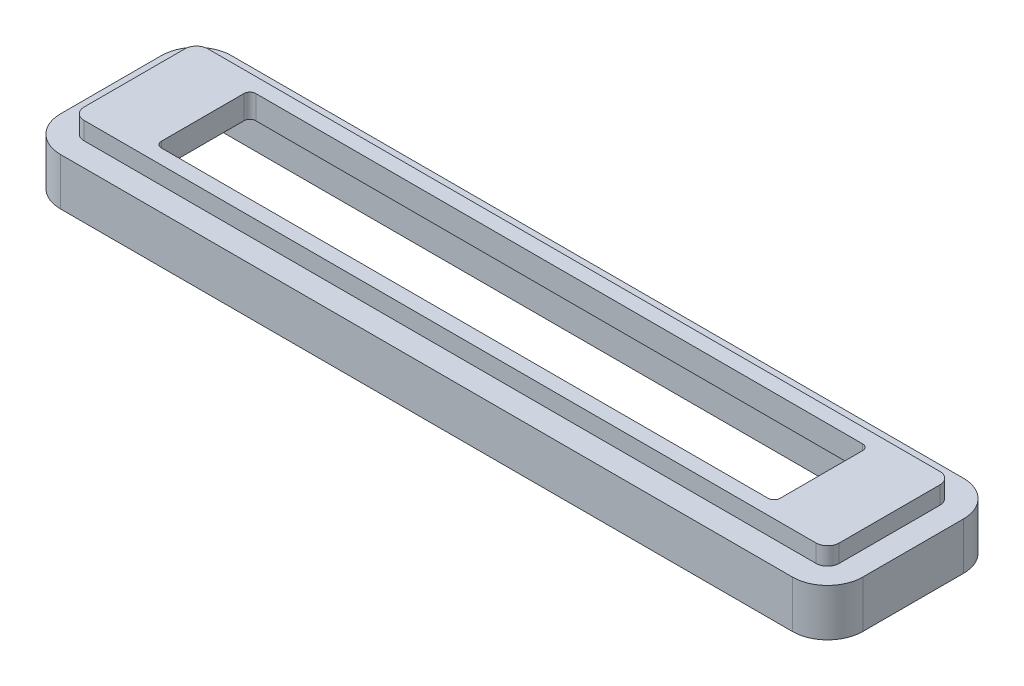
SolidWorks part; units mm, degrees
material "NEOPRENE"
ref_plane "Front Plane" through (0, 0, 0) normal (0, 0, 1) x (1, 0, 0)
ref_plane "Top Plane" through (0, 0, 0) normal (0, 1, 0) x (1, 0, 0)
ref_plane "Right Plane" through (0, 0, 0) normal (1, 0, 0) x (0, 0, -1)
sketch "Sketch1" plane through (0, 0, 0) normal (0, 1, 0) x (1, 0, 0)
  line L0 (-26.215, 3.5) -> (-26.215, -3.5)
  line L1 (-31.0185, -5.25) -> (31.0185, -5.25)
  line L2 (-32, -4.2685) -> (-32, 4.2685)
  line L3 (-31.0185, 5.25) -> (31.0185, 5.25)
  line L4 (32, -4.2685) -> (32, 4.2685)
  line L5 (-32, -5.25) -> (32, 5.25) construction
  line L6 (-32, 5.25) -> (32, -5.25) construction
  line L7 (-25.865, 3.65) -> (25.865, 3.65) construction
  line L8 (-25.865, 3.65) -> (-25.865, -3.65) construction
  line L9 (-25.865, -3.65) -> (25.865, -3.65) construction
  line L10 (25.865, 3.65) -> (25.865, -3.65) construction
  line L11 (-25.865, 3.65) -> (25.865, -3.65) construction
  line L12 (-25.865, -3.65) -> (25.865, 3.65) construction
  line L13 (-25.715, -4) -> (25.715, -4)
  line L14 (26.215, 3.5) -> (26.215, -3.5)
  line L15 (-25.715, 4) -> (25.715, 4)
  line L16 (-26.215, -4) -> (26.215, -4) construction
  line L17 (26.215, 4) -> (26.215, -4) construction
  line L18 (-26.215, 4) -> (26.215, 4) construction
  line L19 (-26.215, 4) -> (-26.215, -4) construction
  arc A0 (31.0185, -5.25) -> (32, -4.2685) centre (31.0185, -4.2685) ccw
  arc A1 (32, 4.2685) -> (31.0185, 5.25) centre (31.0185, 4.2685) ccw
  arc A2 (-31.0185, -5.25) -> (-32, -4.2685) centre (-31.0185, -4.2685) cw
  arc A3 (-32, 4.2685) -> (-31.0185, 5.25) centre (-31.0185, 4.2685) cw
  arc A4 (25.715, -4) -> (26.215, -3.5) centre (25.715, -3.5) ccw
  arc A5 (26.215, 3.5) -> (25.715, 4) centre (25.715, 3.5) ccw
  arc A6 (-26.215, 3.5) -> (-25.715, 4) centre (-25.715, 3.5) cw
  arc A7 (-26.215, -3.5) -> (-25.715, -4) centre (-25.715, -3.5) ccw
  point P0 (0, 0)
  point P18 (0, 0)
  line B0 (26.855, -3.65) -> (26.855, 3.65) construction
  line B1 (-26.855, 3.65) -> (-26.855, -3.65) construction
  line B2 (26.855, 3.65) -> (-26.855, 3.65) construction
  line B3 (-26.855, -3.65) -> (26.855, -3.65) construction
  line B4 (27.205, 1.55) -> (27.205, -1.55) construction
  line B5 (27.205, -3.5) -> (27.205, -1.55) construction
  line B6 (26.055, -4) -> (26.705, -4) construction
  line B7 (-26.055, -4) -> (26.055, -4) construction
  line B8 (-26.705, -4) -> (-26.055, -4) construction
  line B9 (-27.205, -1.55) -> (-27.205, -3.5) construction
  line B10 (-27.205, 1.5499) -> (-27.205, -1.55) construction
  line B11 (-27.205, 3.5) -> (-27.205, 1.5499) construction
  line B12 (-26.055, 4) -> (-26.705, 4) construction
  line B13 (26.055, 4) -> (-26.055, 4) construction
  line B14 (26.705, 4) -> (26.055, 4) construction
  line B15 (27.205, 1.55) -> (27.205, 3.5) construction
  arc B16 (26.705, -4) -> (27.205, -3.5) centre (26.705, -3.5) ccw construction
  arc B17 (-26.705, -4) -> (-27.205, -3.5) centre (-26.705, -3.5) cw construction
  arc B18 (-27.205, 3.5) -> (-26.705, 4) centre (-26.705, 3.5) cw construction
  arc B19 (27.205, 3.5) -> (26.705, 4) centre (26.705, 3.5) ccw construction
  dimension "D3" = 0.9815
  dimension "D6" = 0.5
  dimension "D1" = 64
  dimension "D2" = 10.5
  dimension "D4" = 51.73
  dimension "D5" = 0.35
sketch_block_instance "Block1-1"
sketch_block "Block1" parameters "D2"=0.5, "D3"=2.1, "D1"=0.35
extrude "Boss-Extrude1" add sketch "Sketch1" along normal blind 2
sketch "Sketch2" plane through (0, 0, 0) normal (0, 1, 0) x (1, 0, 0)
  line L0 (-31.0185, -7.25) -> (31.0185, -7.25)
  line L1 (34, -4.2685) -> (34, 4.2685)
  line L2 (31.0185, 7.25) -> (-31.0185, 7.25)
  line L3 (-34, 4.2685) -> (-34, -4.2685)
  line L4 (-31.0185, -5.25) -> (31.0185, -5.25)
  line L5 (-32, 4.2685) -> (-32, -4.2685)
  line L6 (31.0185, 5.25) -> (-31.0185, 5.25)
  line L7 (32, -4.2685) -> (32, 4.2685)
  line L8 (-31.0185, -5.25) -> (31.0185, -5.25)
  line L9 (-32, 4.2685) -> (-32, -4.2685)
  line L10 (31.0185, 5.25) -> (-31.0185, 5.25)
  line L11 (32, -4.2685) -> (32, 4.2685)
  arc A0 (31.0185, -7.25) -> (34, -4.2685) centre (31.0185, -4.2685) ccw
  arc A1 (34, 4.2685) -> (31.0185, 7.25) centre (31.0185, 4.2685) ccw
  arc A2 (-31.0185, 7.25) -> (-34, 4.2685) centre (-31.0185, 4.2685) ccw
  arc A3 (-34, -4.2685) -> (-31.0185, -7.25) centre (-31.0185, -4.2685) ccw
  arc A4 (31.0185, -5.25) -> (32, -4.2685) centre (31.0185, -4.2685) ccw
  arc A5 (-32, -4.2685) -> (-31.0185, -5.25) centre (-31.0185, -4.2685) ccw
  arc A6 (-31.0185, 5.25) -> (-32, 4.2685) centre (-31.0185, 4.2685) ccw
  arc A7 (32, 4.2685) -> (31.0185, 5.25) centre (31.0185, 4.2685) ccw
  arc A8 (31.0185, -5.25) -> (32, -4.2685) centre (31.0185, -4.2685) ccw
  arc A9 (-32, -4.2685) -> (-31.0185, -5.25) centre (-31.0185, -4.2685) ccw
  arc A10 (-31.0185, 5.25) -> (-32, 4.2685) centre (-31.0185, 4.2685) ccw
  arc A11 (32, 4.2685) -> (31.0185, 5.25) centre (31.0185, 4.2685) ccw
  dimension "D1" = 0
  dimension "D2" = 2
extrude "Boss-Extrude2" add sketch "Sketch2" against normal blind 4 from offset 0.5
